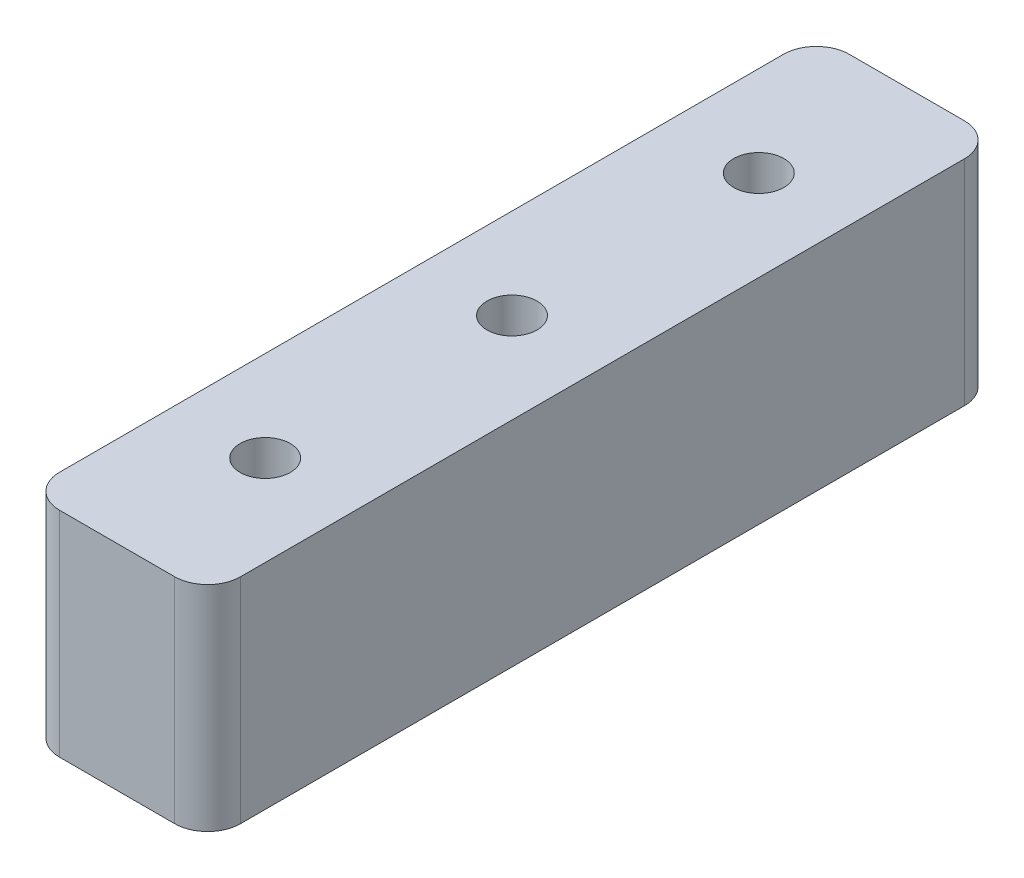
SolidWorks part; units mm, degrees
material "ABS"
ref_plane "前视基准面" through (0, 0, 0) normal (0, 0, 1) x (1, 0, 0)
ref_plane "上视基准面" through (0, 0, 0) normal (0, 1, 0) x (1, 0, 0)
ref_plane "右视基准面" through (0, 0, 0) normal (1, 0, 0) x (0, 0, -1)
other "Configuration Table"
sketch "草图1" plane through (0, 0, 0) normal (0, 1, 0) x (1, 0, 0)
  line L1 (-5.5, -24) -> (5.5, -24)
  line L2 (-5.5, -24) -> (-5.5, 24)
  line L3 (-5.5, 24) -> (5.5, 24)
  line L4 (5.5, -24) -> (5.5, 24)
  line L5 (-5.5, -24) -> (5.5, 24) construction
  line L6 (-5.5, 24) -> (5.5, -24) construction
  point P0 (0, 0)
  dimension "D1" = 11
  dimension "D2" = 48
extrude "凸台-拉伸1" add sketch "草图1" along normal blind 13
sketch "草图2" plane through (0, 13, 0) normal (0, 1, 0) x (1, 0, 0)
  line L0 (2.5, 24) -> (2.5, 50024) construction
  line L1 (-8.5, 0) -> (-8.5, 50000) construction
  line L2 (5.5, -24) -> (5.5, 24) construction
  line L3 (0, 0) -> (50000, 0) construction
  circle A0 centre (2.5, 0) radius 1.525
  circle A1 centre (2.5, 20) radius 1.525
  circle A2 centre (-8.5, 0) radius 1.525
  circle A3 centre (-8.5, 15) radius 1.525
  circle A4 centre (2.5, -20) radius 1.525
  circle A5 centre (-8.5, -15) radius 1.525
  dimension "D2" = 3.05
  dimension "D3" = 20
  dimension "D1" = 3
  dimension "D4" = 11
  dimension "D5" = 15
fillet "圆角1" radius 2 4 edges at (-5.5, 6.5, -24) (5.5, 6.5, 24) (-5.5, 6.5, 24) (5.5, 6.5, -24)
sketch "草图5" plane through (0, 13, 0) normal (0, 1, 0) x (1, 0, 0)
  line L0 (0, 0.2399) -> (0, 50000.2399) construction
  line L1 (0, 0) -> (49380.9275, 0) construction
  circle A0 centre (0, 0) radius 1.525
  circle A1 centre (0, 15) radius 1.525
  circle A2 centre (0, -15) radius 1.525
  dimension "D1" = 3.05
  dimension "D2" = 15
extrude "切除-拉伸1" cut sketch "草图5" against normal through all
